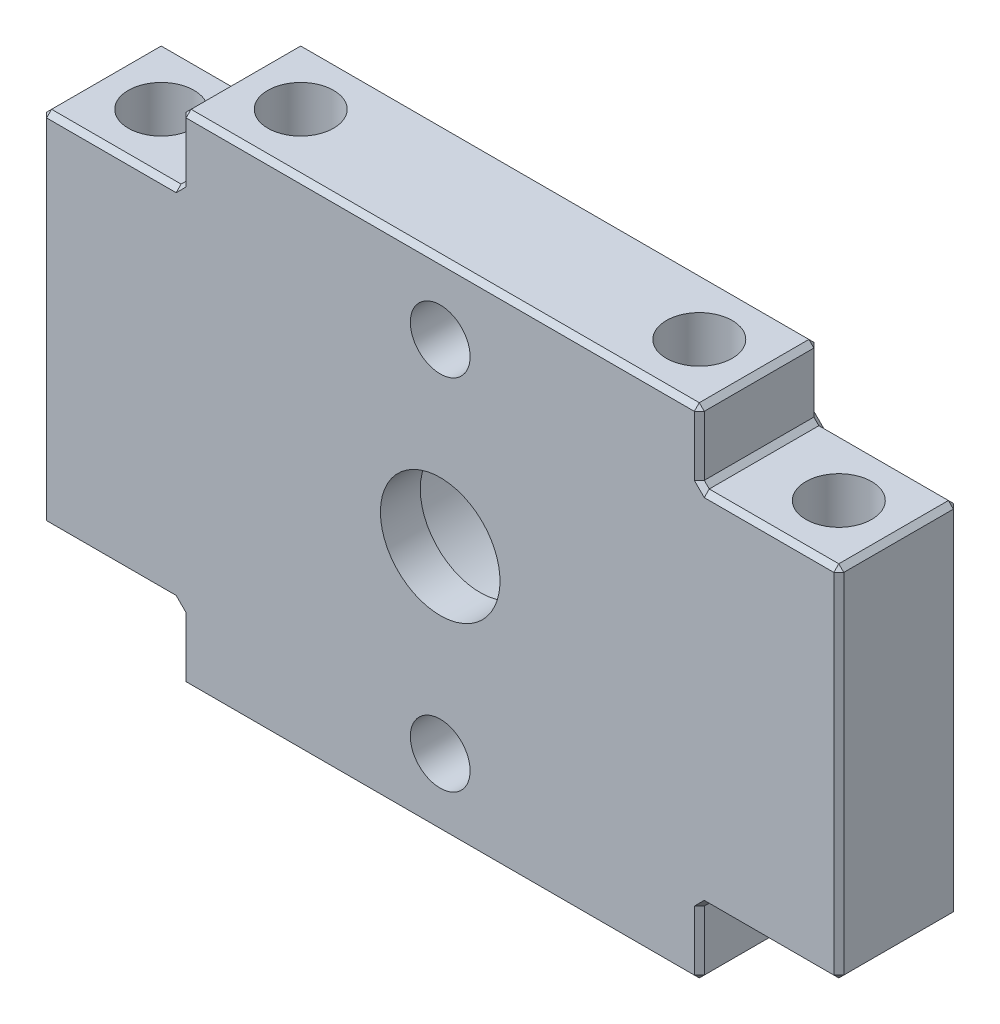
SolidWorks part; units mm, degrees
material "1060 Alloy"
ref_plane "Front Plane" through (0, 0, 0) normal (0, 0, 1) x (1, 0, 0)
ref_plane "Top Plane" through (0, 0, 0) normal (0, 1, 0) x (1, 0, 0)
ref_plane "Right Plane" through (0, 0, 0) normal (1, 0, 0) x (0, 0, -1)
sketch "Sketch1" plane through (0, 0, 0) normal (0, 1, 0) x (1, 0, 0)
  line L0 (-13, -3) -> (13, 3) construction
  line L1 (-13, 3) -> (13, 3)
  line L2 (-13, 3) -> (-13, -3)
  line L3 (-13, -3) -> (13, -3)
  line L4 (13, 3) -> (13, -3)
  point P4 (0, 0)
  dimension "D1" = 6
  dimension "D2" = 26
extrude "Extrude1" add sketch "Sketch1" along normal blind 25
sketch "Sketch2" plane through (0, 0, -3) normal (0, 0, -1) x (-1, 0, 0)
  line L0 (-13, 0) -> (13, 25) construction
  circle A0 centre (0, 12.5) radius 5
  dimension "D1" = 10
extrude "Cut-Extrude1" cut sketch "Sketch2" against normal blind 4
sketch "Sketch3" plane through (0, 0, 1) normal (0, 0, -1) x (-1, 0, 0)
  circle A0 centre (0, 12.5) radius 3
  circle A1 centre (0, 12.5) radius 5 construction
  dimension "D1" = 6
extrude "Cut-Extrude2" cut sketch "Sketch3" against normal blind 12
hole_wizard "M4x0.7 Tapped Hole1" positions "3DSketch1" profile "Sketch5" tap size "M4x0.7" standard "Ansi Metric"
sketch3d "3DSketch1"
  line L0 (-12.7688, 25, -3) -> (-12.7688, 25, 3) construction
  line L1 (13, 25, -3) -> (-13, 25, -3) construction
  line L2 (-13, 25, 3) -> (13, 25, 3) construction
  line L3 (-13, 25, -3) -> (-13, 25, 3) construction
  line L4 (13, 25, 3) -> (13, 25, -3) construction
  point P0 (10, 25, 0)
  point P2 (-10, 25, 0)
  point P5 (10, 0, 0)
  point P7 (-10, 0, 0)
  point P17 (-12.7688, 25, 0)
  dimension "D1" = 3
  dimension "D2" = 3
sketch "Sketch5" plane through (10, 25, 0) normal (1, 0, 0) x (0, 0, 1)
  line L0 (0, 0) -> (0, 11.2914)
  line L1 (0, 11.2914) -> (1.65, 10.3)
  line L2 (1.65, 10.3) -> (1.65, 0)
  line L5 (1.65, 0) -> (0, 0)
  line L10 (0, 11.2914) -> (-1.65, 10.3) construction
  line L11 (0, -6.35) -> (0, 107.95) construction
  dimension "Tap Drill Dia." = 3.3
  dimension "Tap Drill Depth" = 10.3
  dimension "Drill Angle" = 118
cosmetic thread "Hole Thread1" parameters "D1"=8.2, "D2"=4
cosmetic thread "Hole Thread2" parameters "D1"=8.2, "D2"=4
cosmetic thread "Hole Thread3" parameters "D1"=8.2, "D2"=4
cosmetic thread "Hole Thread4" parameters "D1"=8.2, "D2"=4
sketch "Sketch7" plane through (0, 0, 3) normal (0, 0, 1) x (1, 0, 0)
  circle A0 centre (0, 21.5) radius 1.5
  circle A1 centre (0, 3.5) radius 1.5
  dimension "D1" = 3
  dimension "D2" = 3
  dimension "D3" = 9
  dimension "D4" = 9
extrude "Cut-Extrude3" cut sketch "Sketch7" against normal blind 10
chamfer "Chamfer2" distance 1 angle 45 2 edges at (1.5, 3.5, -3) (1.5, 21.5, -3)
sketch "Sketch8" plane through (0, 0, 3) normal (0, 0, 1) x (1, 0, 0)
  line L0 (13, 25) -> (13, 0) construction
  line L1 (13, 3.5) -> (20, 3.5)
  line L2 (13, 3.5) -> (13, 21.5)
  line L3 (13, 21.5) -> (20, 21.5)
  line L4 (20, 3.5) -> (20, 21.5)
  line L5 (-13, 25) -> (-13, 0) construction
  line L6 (-13, 0) -> (13, 0) construction
  line L10 (-13, 21.5) -> (-20, 21.5)
  line L11 (-13, 21.5) -> (-13, 3.5)
  line L12 (-13, 3.5) -> (-20, 3.5)
  line L13 (-20, 21.5) -> (-20, 3.5)
  dimension "D1" = 18
  dimension "D2" = 18
  dimension "D3" = 3.5
  dimension "D4" = 7
  dimension "D5" = 7
extrude "Extrude2" add sketch "Sketch8" against normal up to surface (6 mm away) up to face at (2.5, 3.5, -3)
hole_wizard "M4x0.7 Tapped Hole2" positions "3DSketch2" profile "Sketch9" tap size "M4x0.7" standard "Ansi Metric"
sketch3d "3DSketch2"
  line L0 (-20, 21.5, -3) -> (-20, 21.5, 3) construction
  line L1 (-20, 21.5, -3) -> (-13, 21.5, -3) construction
  line L2 (20, 21.5, -3) -> (20, 21.5, 3) construction
  point P0 (-17, 21.5, 0)
  point P2 (17, 21.5, 0)
  point P4 (17, 3.5, 0)
  point P6 (-17, 3.5, 0)
  dimension "D1" = 3
  dimension "D2" = 3
  dimension "D3" = 3
sketch "Sketch9" plane through (-17, 21.5, 0) normal (1, 0, 0) x (0, 0, 1)
  line L0 (0, 0) -> (0, 8.9914)
  line L1 (0, 8.9914) -> (1.65, 8)
  line L2 (1.65, 8) -> (1.65, 0)
  line L5 (1.65, 0) -> (0, 0)
  line L10 (0, 8.9914) -> (-1.65, 8) construction
  line L11 (0, -6.35) -> (0, 107.95) construction
  dimension "Tap Drill Dia." = 3.3
  dimension "Tap Drill Depth" = 8
  dimension "Drill Angle" = 118
cosmetic thread "Hole Thread5" parameters "D1"=6, "D2"=4
cosmetic thread "Hole Thread6" parameters "D1"=6, "D2"=4
cosmetic thread "Hole Thread7" parameters "D1"=6, "D2"=4
cosmetic thread "Hole Thread8" parameters "D1"=6, "D2"=4
chamfer "Chamfer3" distance 0.25 angle 45 36 edges at (13, 25, 0) (-13, 0, 0) (13, 0, 0) (0, 0, 3) (20, 3.5, 0) (20, 12.5, 3) (20, 21.5, 0) (20, 12.5, -3) (0, 0, -3) (-20, 21.5, 0) (-20, 12.5, 3) (-20, 3.5, 0) (-20, 12.5, -3) (0, 25, -3) (-13, 25, 0) (0, 25, 3)
